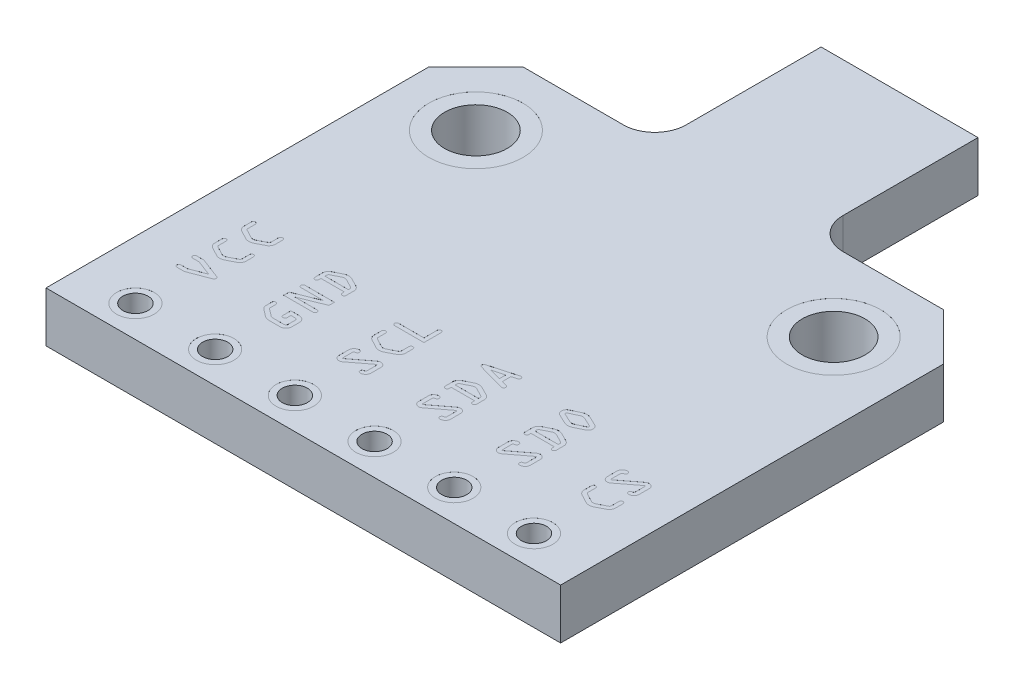
SolidWorks part; units mm, degrees
material "A-Glass Fiber"
ref_plane "Front Plane" through (0, 0, 0) normal (0, 0, 1) x (1, 0, 0)
ref_plane "Top Plane" through (0, 0, 0) normal (0, 1, 0) x (1, 0, 0)
ref_plane "Right Plane" through (0, 0, 0) normal (1, 0, 0) x (0, 0, -1)
sketch "BaseS" plane through (0, 0, 0) normal (0, 1, 0) x (1, 0, 0)
  line L0 (-2.5, 6.85) -> (-2.5, 12.15)
  line L1 (-8.2, 6.85) -> (-2.5, 6.85)
  line L2 (-8.2, 6.85) -> (-8.2, -6.85)
  line L3 (-8.2, -6.85) -> (8.2, -6.85)
  line L4 (8.2, 6.85) -> (8.2, -6.85)
  line L5 (-8.2, 6.85) -> (8.2, -6.85) construction
  line L6 (-8.2, -6.85) -> (8.2, 6.85) construction
  line L7 (-2.5, 12.15) -> (2.5, 12.15)
  line L8 (2.5, 12.15) -> (2.5, 6.85)
  line L9 (0, 0) -> (0, 12.15) construction
  line L10 (2.5, 6.85) -> (8.2, 6.85)
  point P0 (0, 0)
  dimension "Width1" = 16.4
  dimension "Length1" = 13.7
  dimension "Width2" = 5
  dimension "Length2" = 5.3
extrude "Base" add sketch "BaseS" along normal mid plane 1.6
sketch "FasteningHoleS" plane through (0, 0.8, 0) normal (0, 1, 0) x (1, 0, 0)
  line L0 (-8.2, 6.85) -> (-8.2, -6.85) construction
  line L1 (-2.5, 6.85) -> (-8.2, 6.85) construction
  circle A0 centre (-5.7, 4.35) radius 1
  dimension "Dia" = 2
  dimension "XDim" = 2.5
  dimension "YDim" = 2.5
extrude "FasteningHole" cut sketch "FasteningHoleS" against normal through all
sketch "FHSolderCutS" plane through (0, 0.8, 0) normal (0, 1, 0) x (1, 0, 0)
  circle A0 centre (-5.7, 4.35) radius 1 construction
  circle A1 centre (-5.7, 4.35) radius 1
  circle A2 centre (-5.7, 4.35) radius 1.5
  dimension "Offset" = 0.5
extrude "FHSolderCut" cut sketch "FHSolderCutS" against normal blind 0.001
mirror "FHSCVM" about plane through (0, 0, 0) normal (0, 1, 0) of "FHSolderCut"
mirror "FHHM" about plane through (0, 0, 0) normal (1, 0, 0) of "FHSCVM", "FHSolderCut", "FasteningHole"
sketch "PinHoleS" plane through (0, 0.8, 0) normal (0, 1, 0) x (1, 0, 0)
  line L0 (-8.2, 6.85) -> (-8.2, -6.85) construction
  line L1 (-8.2, -6.85) -> (8.2, -6.85) construction
  circle A0 centre (-6.35, -5.85) radius 0.4
  dimension "Dia" = 0.8
  dimension "XDim" = 1.85
  dimension "YDim" = 1
extrude "PinHole" cut sketch "PinHoleS" against normal through all
sketch "PHSolderCutS" plane through (0, 0.8, 0) normal (0, 1, 0) x (1, 0, 0)
  circle A0 centre (-6.35, -5.85) radius 0.6
  circle A1 centre (-6.35, -5.85) radius 0.4 construction
  circle A2 centre (-6.35, -5.85) radius 0.4
  dimension "Width" = 0.2
extrude "PHSolderCut" cut sketch "PHSolderCutS" against normal blind 0.001
mirror "PHSCVM" about plane through (0, 0, 0) normal (0, 1, 0) of "PHSolderCut"
pattern_linear "PHLP" count 6 spacing 2.54 along (1, 0, 0) of "PinHole", "PHSolderCut", "PHSCVM"
chamfer "BaseC" distance 1.5 angle 45 2 edges at (-8.2, 0, -6.85) (8.2, 0, -6.85)
fillet "BaseF" radius 1 2 edges at (-2.5, 0, -6.85) (2.5, 0, -6.85)
sketch "TextLayoutLinesS" plane through (0, 0.8, 0) normal (0, 1, 0) x (1, 0, 0)
  line L0 (-5.75, -4.35) -> (-5.75, -0.35) construction
  line L1 (-8.2, -6.85) -> (8.2, -6.85) construction
  line L2 (-3.21, -0.35) -> (-3.21, -4.35) construction
  line L3 (-5.75, -4.35) -> (-3.21, -4.35) construction
  line L4 (-0.67, -0.35) -> (-0.67, -4.35) construction
  line L5 (-3.21, -4.35) -> (-0.67, -4.35) construction
  line L6 (-0.67, -4.35) -> (1.87, -4.35) construction
  line L7 (1.87, -4.35) -> (1.87, -0.35) construction
  line L8 (1.87, -4.35) -> (4.41, -4.35) construction
  line L9 (4.41, -4.35) -> (4.41, -0.35) construction
  line L10 (4.41, -4.35) -> (6.95, -4.35) construction
  line L11 (6.95, -4.35) -> (6.95, -0.35) construction
  circle A0 centre (-6.35, -5.85) radius 0.6 construction
  circle A1 centre (-3.81, -5.85) radius 0.6 construction
  circle A2 centre (-1.27, -5.85) radius 0.6 construction
  circle A3 centre (1.27, -5.85) radius 0.6 construction
  circle A4 centre (3.81, -5.85) radius 0.6 construction
  circle A5 centre (6.35, -5.85) radius 0.6 construction
  dimension "D1" = 4
  dimension "D2" = 2.5
sketch "TextS" plane through (0, 0.8, 0) normal (0, 1, 0) x (1, 0, 0)
  text T0 "VCC" font "OCR A Extended" height 1
  text T1 "GND" font "OCR A Extended" height 1
  text T2 "SCL" font "OCR A Extended" height 1
  text T3 "SDA" font "OCR A Extended" height 1
  text T4 "SDO" font "OCR A Extended" height 1
  text T5 "CS" font "OCR A Extended" height 1
extrude "Text" cut sketch "TextS" against normal blind 0.001
sketch "TextRotationAxis" plane through (0, 0, 0) normal (0, 1, 0) x (1, 0, 0)
  line L0 (-8.2, -3.0071) -> (8.2, -3.0071) construction
  line L1 (-8.2, 5.35) -> (-8.2, -6.85) construction
  line L2 (8.2, -6.85) -> (8.2, 5.35) construction
  line L3 (0.9986, -3.0071) -> (1.7414, -3.0071) construction
  point P8 (0, -3.0071)
pattern_circular "TextCP" count 2 over 360 about axis through (-8.2, 0, 3.0071) along (1, 0, 0) of "Text"
sketch "PartNoTextS" plane through (0, -0.8, 0) normal (0, -1, 0) x (1, 0, 0)
  line L0 (8.2, -1.15) -> (-8.2, -1.15) construction
  line L1 (-8.2, -5.35) -> (-8.2, 6.85) construction
  line L2 (8.2, 6.85) -> (8.2, -5.35) construction
  line L3 (-8.2, 6.85) -> (8.2, 6.85) construction
  text T0 "BME680" font "OCR A Extended" height 1
  point P3 (-8.2, 0.3506)
  point P6 (8.2, 0.2976)
  point P11 (8.3343, -1.15)
  dimension "YDim" = 8
extrude "PartNoText" cut sketch "PartNoTextS" against normal blind 0.001
